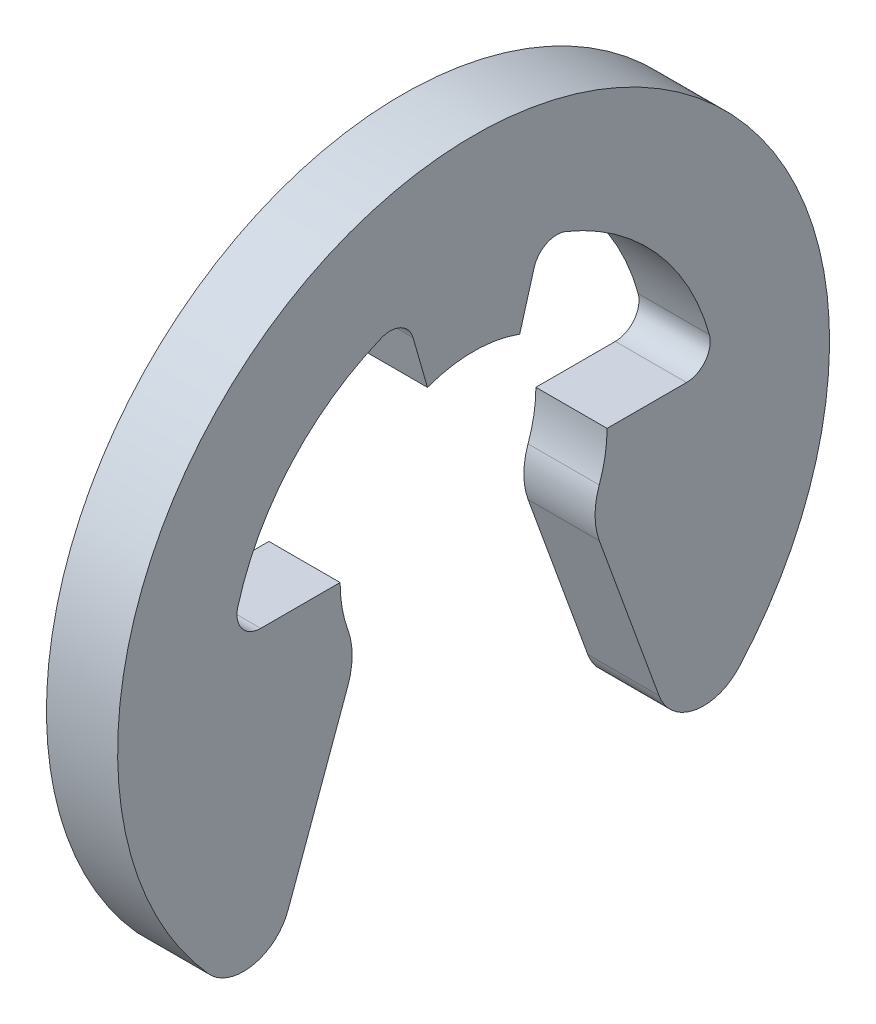
SolidWorks part; units mm, degrees
material "Acier allié"
ref_plane "Plan1" through (0, 0, 0) normal (0, 0, 1) x (1, 0, 0)
ref_plane "Plan2" through (0, 0, 0) normal (0, 1, 0) x (1, 0, 0)
ref_plane "Plan3" through (0, 0, 0) normal (1, 0, 0) x (0, 0, -1)
sketch "Esquisse1" plane through (0, 0, 0) normal (1, 0, 0) x (0, 0, -1)
  line L0 (0, 0) -> (7.4907, -18.9647) construction
  line L1 (0, 0) -> (0, -9.1601) construction
  line L2 (-20, 0) -> (20, 0) construction
  line L3 (0, 0) -> (0.5513, 1.9225) construction
  line L4 (-20, 0.2) -> (20, 0.2) construction
  line L5 (0.2592, 0.9038) -> (7.4907, -18.9647) construction
  line L6 (0.2592, 0.9038) -> (0.3403, 1.1867)
  line L7 (-0.75, 0.2) -> (-1.1961, 0.2)
  line L8 (0.7065, -0.3253) -> (1.0417, -1.2463)
  line L9 (0.75, 0.2) -> (1.1961, 0.2)
  line L10 (-0.7065, -0.3253) -> (-1.0417, -1.2463)
  line L11 (-0.2592, 0.9038) -> (-0.3403, 1.1867)
  arc A0 (1.4912, -1.3328) -> (-1.4912, -1.3328) centre (0, 0) ccw
  arc A1 (1.3245, 0.3691) -> (0.5187, 1.2734) centre (0, 0) ccw
  arc A2 (0.2592, 0.9038) -> (-0.2592, 0.9038) centre (0, 0.2) ccw
  arc A3 (0.75, 0.2) -> (0.7059, -0.0534) centre (0, 0.2) cw
  arc A4 (1.4912, -1.3328) -> (1.0417, -1.2463) centre (1.2923, -1.1551) cw
  arc A5 (0.5187, 1.2734) -> (0.3403, 1.1867) centre (0.4684, 1.1499) ccw
  arc A6 (1.3245, 0.3691) -> (1.1961, 0.2) centre (1.1961, 0.3333) cw
  arc A7 (-1.3245, 0.3691) -> (-1.1961, 0.2) centre (-1.1961, 0.3333) ccw
  arc A8 (-0.5187, 1.2734) -> (-0.3403, 1.1867) centre (-0.4684, 1.1499) cw
  arc A9 (-1.4912, -1.3328) -> (-1.0417, -1.2463) centre (-1.2923, -1.1551) ccw
  arc A10 (-0.75, 0.2) -> (-0.7059, -0.0534) centre (0, 0.2) ccw
  arc A11 (-1.3245, 0.3691) -> (-0.5187, 1.2734) centre (0, 0) cw
  arc A12 (0.7065, -0.3253) -> (0.7059, -0.0534) centre (1.0824, -0.1885) cw
  arc A13 (-0.7065, -0.3253) -> (-0.7059, -0.0534) centre (-1.0824, -0.1885) ccw
  point P24 (3.1354, 10.9344)
  dimension "D1" = 2
  dimension "D2" = 0.2
  dimension "D3" = 1.375
  dimension "D4" = 0.2667
  dimension "D7" = 0.4
  dimension "D8" = 16
  dimension "D9" = 20
extrude "Base-Extrusion" add sketch "Esquisse1" along normal blind 0.4
equation "\"D3@Esquisse1\" = (\"D1@Esquisse1\"+\"dn@Esquisse1\")/2"
equation "\"D4@Esquisse1\"=\"r@Esquisse1\"*2"
equation "\"r@Esquisse1\"=\"D1@Base-Extrusion\"/3"
equation "\"D2@Esquisse1\"=\"D1@Base-Extrusion\"/2"
